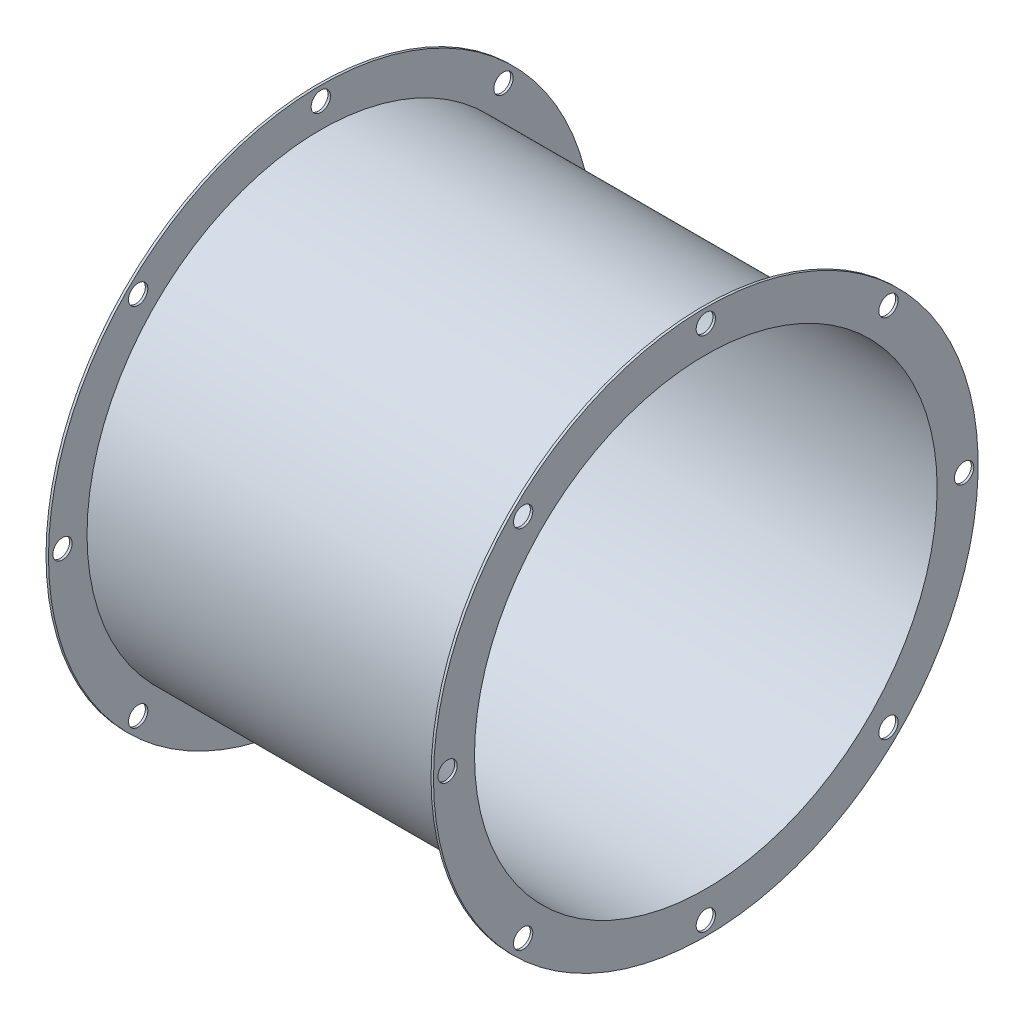
SolidWorks part; units mm, degrees
ref_plane "Front Plane" through (0, 0, 0) normal (0, 0, 1) x (1, 0, 0)
ref_plane "Top Plane" through (0, 0, 0) normal (0, 1, 0) x (1, 0, 0)
ref_plane "Right Plane" through (0, 0, 0) normal (1, 0, 0) x (0, 0, -1)
sketch "Sketch1" plane through (0, 0, 0) normal (0, 0, 1) x (1, 0, 0)
  line L0 (0, 0) -> (43.9716, 0) construction
  line L1 (0, 76.2) -> (127.635, 76.2)
  line L2 (127.635, 76.2) -> (127.635, 89.7128)
  line L3 (127.635, 89.7128) -> (126.8222, 89.7128)
  line L4 (126.8222, 89.7128) -> (126.8222, 77.0128)
  line L5 (126.8222, 77.0128) -> (0.8128, 77.0128)
  line L6 (0.8128, 77.0128) -> (0.8128, 89.7128)
  line L7 (0.8128, 89.7128) -> (0, 89.7128)
  line L8 (0, 89.7128) -> (0, 76.2)
  dimension "D1" = 0.8128
  dimension "D2" = 0.8128
  dimension "D3" = 0.8128
  dimension "D4" = 127.635
  dimension "D5" = 12.7
  dimension "D6" = 12.7
  dimension "D7" = 152.4
revolve "Revolve1" add sketch "Sketch1" angle 360 about L0
sketch "Sketch2" plane through (0, 0, 0) normal (1, 0, 0) x (0, 0, -1)
  circle A0 centre (0, 85.09) radius 3.175
  dimension "D2" = 6.35
  dimension "D1" = 85.09
extrude "Cut-Extrude1" cut sketch "Sketch2" along normal blind 224.79
pattern_circular "CirPattern1" count 8 over 360 about axis through (0, 0, 0) along (1, 0, 0) of "Cut-Extrude1"
